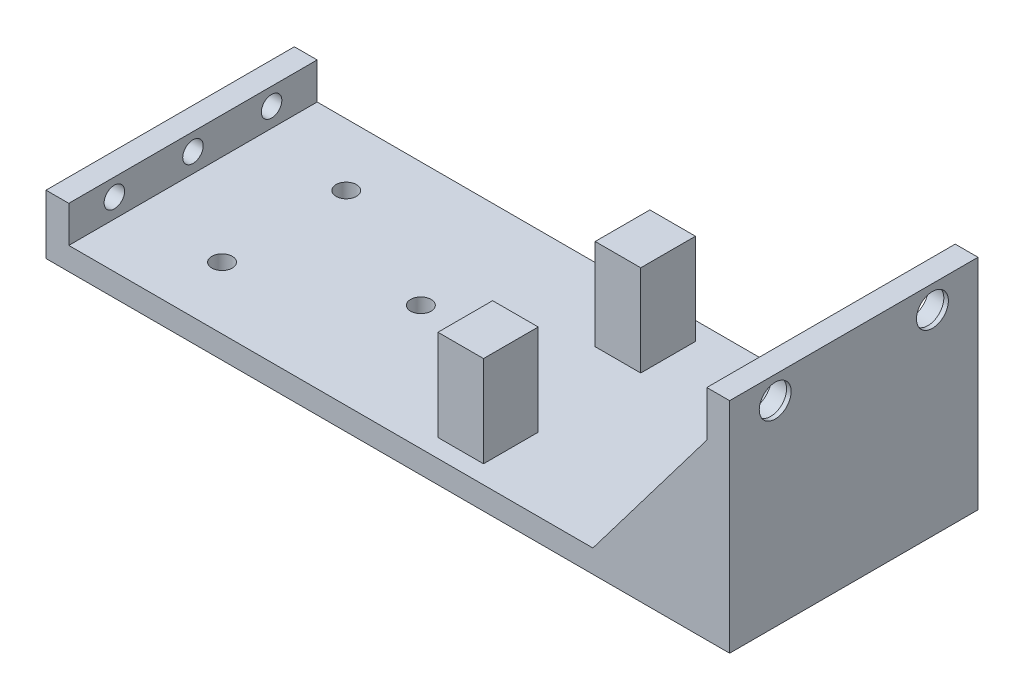
SolidWorks part; units mm, degrees
ref_plane "Front Plane" through (0, 0, 0) normal (0, 0, 1) x (1, 0, 0)
ref_plane "Top Plane" through (0, 0, 0) normal (0, 1, 0) x (1, 0, 0)
ref_plane "Right Plane" through (0, 0, 0) normal (1, 0, 0) x (0, 0, -1)
sketch "Sketch1" plane through (0, 0, 0) normal (0, 1, 0) x (1, 0, 0)
  line L2 (56.8875, -28.9394) -> (-93.1125, -28.9394)
  line L3 (56.8875, -28.9394) -> (56.8875, 25.5606)
  line L4 (56.8875, 25.5606) -> (-93.1125, 25.5606)
  line L5 (-93.1125, -28.9394) -> (-93.1125, 25.5606)
  dimension "D1" = 150
  dimension "D2" = 54.5
extrude "Boss-Extrude1" add sketch "Sketch1" along normal blind 5
sketch "Sketch2" plane through (0, 5, 0) normal (0, 1, 0) x (1, 0, 0)
  line L0 (-93.1125, -28.9394) -> (56.8875, -28.9394) construction
  line L1 (-93.1125, 25.5606) -> (-88.1125, 25.5606)
  line L2 (-93.1125, 25.5606) -> (-93.1125, -28.9394)
  line L3 (-93.1125, -28.9394) -> (-88.1125, -28.9394)
  line L4 (-88.1125, 25.5606) -> (-88.1125, -28.9394)
  dimension "D1" = 5
extrude "Boss-Extrude2" add sketch "Sketch2" along normal blind 8
hole_wizard "#8 Clearance Hole1" positions "3DSketch1" profile "Sketch3" hole size "#8" standard "ANSI Inch"
sketch3d "3DSketch1"
  line L1 (-93.1125, 13, -25.5606) -> (-93.1125, 13, 28.9394) construction
  line L2 (-93.1125, 13, -25.5606) -> (-93.1125, 0, -25.5606) construction
  line L3 (-93.1125, 13, 28.9394) -> (-93.1125, 0, 28.9394) construction
  point P0 (-93.1125, 9.2, -15.5606)
  point P2 (-93.1125, 9.2, 1.6894)
  point P4 (-93.1125, 9.2, 18.9394)
  dimension "D1" = 3.8
  dimension "D2" = 3.8
  dimension "D3" = 3.8
  dimension "D4" = 10
  dimension "D5" = 27.25
  dimension "D6" = 10
sketch "Sketch3" plane through (-93.1125, 9.2, -15.5606) normal (0, 1, 0) x (0, 0, 1)
  line L0 (0, 0) -> (0, 18.3507)
  line L1 (0, 18.3507) -> (2.2479, 17)
  line L2 (2.2479, 17) -> (2.2479, 0)
  line L5 (2.2479, 0) -> (0, 0)
  line L10 (0, 18.3507) -> (-2.2479, 17) construction
  line L11 (0, -6.35) -> (0, 107.95) construction
  dimension "Hole Dia." = 4.4958
  dimension "Hole Depth" = 17
  dimension "Drill Angle" = 118
sketch "Sketch7" plane through (0, 5, 0) normal (0, 1, 0) x (1, 0, 0)
  line L0 (56.8875, 25.5606) -> (-88.1125, 25.5606) construction
  line L1 (56.8875, -28.9394) -> (51.8875, -28.9394)
  line L2 (56.8875, -28.9394) -> (56.8875, 25.5606)
  line L3 (56.8875, 25.5606) -> (51.8875, 25.5606)
  line L4 (51.8875, -28.9394) -> (51.8875, 25.5606)
  dimension "D1" = 5
extrude "Boss-Extrude3" add sketch "Sketch7" along normal blind 43
sketch "Sketch8" plane through (51.8875, 0, 0) normal (-1, 0, 0) x (0, 0, 1)
  line L0 (-25.5606, 48) -> (28.9394, 48) construction
  line L1 (-25.5606, 48) -> (-25.5606, 5) construction
  line L2 (28.9394, 48) -> (28.9394, 5) construction
  circle A0 centre (-15.5606, 43) radius 4.25
  circle A1 centre (18.9394, 43) radius 4.25
  dimension "D1" = 8.5
  dimension "D2" = 8.5
  dimension "D3" = 5
  dimension "D4" = 5
  dimension "D5" = 10
  dimension "D6" = 10
extrude "Cut-Extrude1" cut sketch "Sketch8" against normal blind 4
sketch "Sketch10" plane through (0, 0, -25.5606) normal (0, 0, -1) x (-1, 0, 0)
  line L0 (-51.8875, 38) -> (-26.8875, 5)
  line L1 (-51.8875, 48) -> (-51.8875, 5) construction
  line L2 (-51.8875, 5) -> (88.1125, 5) construction
  dimension "D1" = 10
  dimension "D2" = 25
rib "Rib1" sketch "Sketch10" sketch "Sketch10" thickness 10 extrusion direction parallel to sketch draft on no parameters "D1"=10
sketch "Sketch12" plane through (0, 0, 28.9394) normal (0, 0, 1) x (1, 0, 0)
  line L0 (51.8875, 38) -> (26.8875, 5)
  line L1 (51.8875, 48) -> (51.8875, 5) construction
  line L2 (-88.1125, 5) -> (51.8875, 5) construction
  dimension "D1" = 10
  dimension "D2" = 25
rib "Rib3" sketch "Sketch12" sketch "Sketch12" thickness 10 extrusion direction parallel to sketch draft on no parameters "D1"=10
sketch "Sketch13" plane through (51.8875, 0, 0) normal (-1, 0, 0) x (0, 0, 1)
  line L0 (-25.5606, 48) -> (28.9394, 48) construction
  line L1 (-2.3106, 38) -> (5.6894, 38)
  line L2 (-2.3106, 38) -> (-2.3106, 36)
  line L3 (-2.3106, 36) -> (5.6894, 36)
  line L4 (5.6894, 38) -> (5.6894, 36)
  line L5 (-25.5606, 48) -> (-25.5606, 38) construction
  line L6 (28.9394, 48) -> (28.9394, 38) construction
  dimension "D1" = 8
  dimension "D2" = 10
  dimension "D3" = 23.25
  dimension "D4" = 23.25
  dimension "D5" = 2
extrude "Boss-Extrude4" add sketch "Sketch13" along normal blind 5
sketch "Sketch14" plane through (0, 38, 0) normal (0, 1, 0) x (1, 0, 0)
  line L0 (46.8875, -5.6894) -> (46.8875, 2.3106) construction
  line L1 (46.8875, 2.3106) -> (51.8875, 2.3106) construction
  circle A0 centre (49.3875, -1.6894) radius 2
  dimension "D1" = 2.5
  dimension "D2" = 4
extrude "Cut-Extrude2" cut sketch "Sketch14" against normal blind 2
sketch "Sketch15" plane through (55.8875, 0, 0) normal (-1, 0, 0) x (0, 0, 1)
  line L0 (28.9394, 48) -> (-25.5606, 48) construction
  circle A0 centre (-15.5606, 43) radius 3.5
  circle A1 centre (18.9394, 43) radius 3.5
  dimension "D1" = 5
  dimension "D2" = 5
extrude "Cut-Extrude3" cut sketch "Sketch15" against normal blind 1
sketch "Sketch16" plane through (0, 5, 0) normal (0, 1, 0) x (1, 0, 0)
  line L0 (56.8875, -28.9394) -> (56.8875, 25.5606) construction
  line L1 (-1.1125, 21.5606) -> (-11.1125, 21.5606)
  line L2 (-1.1125, 21.5606) -> (-1.1125, 9.5606)
  line L3 (-1.1125, 9.5606) -> (-11.1125, 9.5606)
  line L4 (-11.1125, 21.5606) -> (-11.1125, 9.5606)
  line L5 (26.8875, 25.5606) -> (-88.1125, 25.5606) construction
  line L6 (-88.1125, -28.9394) -> (26.8875, -28.9394) construction
  line L7 (-1.1125, -12.9394) -> (-11.1125, -12.9394)
  line L8 (-1.1125, -12.9394) -> (-1.1125, -24.9394)
  line L9 (-1.1125, -24.9394) -> (-11.1125, -24.9394)
  line L10 (-11.1125, -12.9394) -> (-11.1125, -24.9394)
  dimension "D1" = 58
  dimension "D2" = 12
  dimension "D3" = 10
  dimension "D4" = 4
  dimension "D5" = 12
  dimension "D6" = 4
  dimension "D7" = 58
  dimension "D8" = 10
hole_wizard "#8 Clearance Hole2" positions "3DSketch2" profile "Sketch17" hole size "#8" standard "ANSI Inch"
sketch3d "3DSketch2"
  line L1 (26.8875, 5, -25.5606) -> (-88.1125, 5, -25.5606) construction
  line L2 (-88.1125, 5, 28.9394) -> (26.8875, 5, 28.9394) construction
  line L5 (51.8875, 5, -15.5606) -> (51.8875, 5, 18.9394) construction
  point P0 (-38.1125, 5, 1.6894)
  point P2 (-68.1125, 5, 15.3144)
  point P4 (-68.1125, 5, -11.9356)
  dimension "D1" = 13.625
  dimension "D2" = 13.625
  dimension "D3" = 90
  dimension "D5" = 120
  dimension "D4" = 27.25
  dimension "D6" = 120
  dimension "D7" = 27.25
  dimension "D8" = 32.9491
  dimension "D9" = 32.9491
sketch "Sketch17" plane through (-38.1125, 5, 1.6894) normal (1, 0, 0) x (0, 0, 1)
  line L0 (0, 0) -> (0, 18.3507)
  line L1 (0, 18.3507) -> (2.2479, 17)
  line L2 (2.2479, 17) -> (2.2479, 0)
  line L5 (2.2479, 0) -> (0, 0)
  line L10 (0, 18.3507) -> (-2.2479, 17) construction
  line L11 (0, -6.35) -> (0, 107.95) construction
  dimension "Hole Dia." = 4.4958
  dimension "Hole Depth" = 17
  dimension "Drill Angle" = 118
extrude "Boss-Extrude5" add sketch "Sketch16" along normal blind 20
sketch "Sketch18" plane through (-11.1125, 0, 0) normal (-1, 0, 0) x (0, 0, 1)
  line L0 (-21.5606, 25) -> (-21.5606, 5) construction
  line L1 (-19.0606, 23.5) -> (-12.0606, 23.5)
  line L2 (-19.0606, 23.5) -> (-19.0606, 16.5)
  line L3 (-19.0606, 16.5) -> (-12.0606, 16.5)
  line L4 (-12.0606, 23.5) -> (-12.0606, 16.5)
  line L5 (15.4394, 23.5) -> (22.4394, 23.5)
  line L6 (15.4394, 23.5) -> (15.4394, 16.5)
  line L7 (15.4394, 16.5) -> (22.4394, 16.5)
  line L8 (22.4394, 23.5) -> (22.4394, 16.5)
  line L9 (-9.5606, 25) -> (-9.5606, 5) construction
  line L10 (-21.5606, 25) -> (-9.5606, 25) construction
  line L11 (12.9394, 25) -> (12.9394, 5) construction
  line L12 (24.9394, 25) -> (24.9394, 5) construction
  line L13 (12.9394, 25) -> (24.9394, 25) construction
  dimension "D1" = 2.5
  dimension "D2" = 2.5
  dimension "D3" = 1.5
  dimension "D4" = 2.5
  dimension "D5" = 2.5
  dimension "D6" = 1.5
  dimension "D7" = 7
extrude "Cut-Extrude4" cut sketch "Sketch18" against normal blind 8
